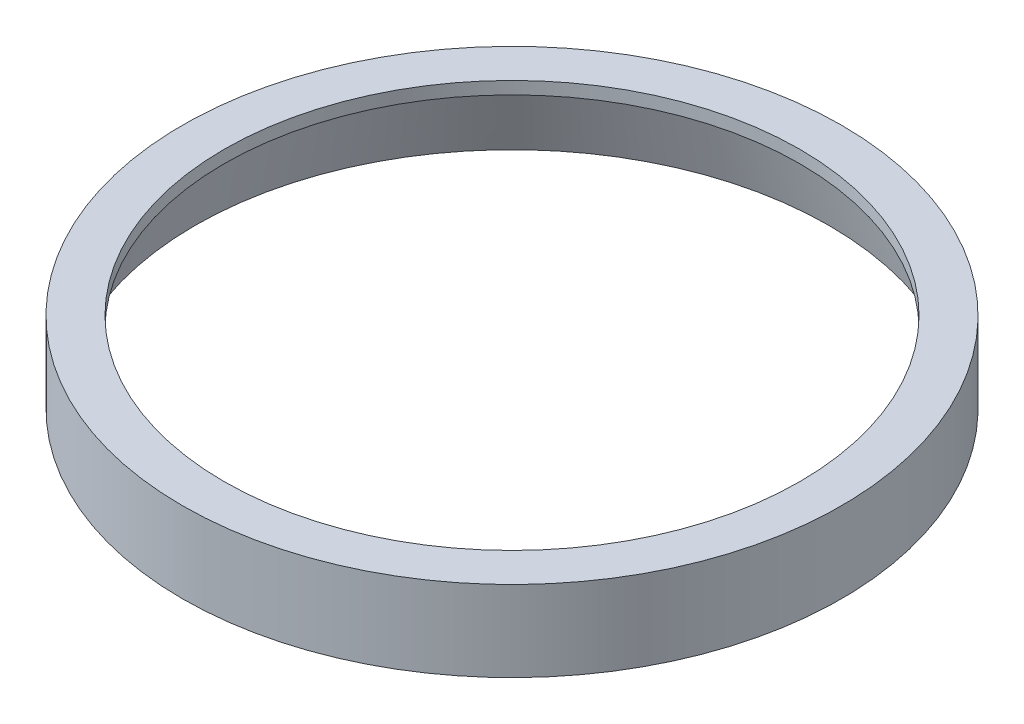
SolidWorks part; units mm, degrees
ref_plane "Front Plane" through (0, 0, 0) normal (0, 0, 1) x (1, 0, 0)
ref_plane "Top Plane" through (0, 0, 0) normal (0, 1, 0) x (1, 0, 0)
ref_plane "Right Plane" through (0, 0, 0) normal (1, 0, 0) x (0, 0, -1)
sketch "Sketch1" plane through (0, 0, 0) normal (0, 0, 1) x (1, 0, 0)
  line L0 (37.5, 0) -> (30.5, 0) construction
  line L1 (30.5, 0) -> (30.5, 1.45) construction
  line L2 (30.5, 1.45) -> (32.5, 1.45) construction
  line L3 (32.5, 1.45) -> (32.5, 8) construction
  line L4 (37.5, 0) -> (37.5, 2.2679) construction
  line L5 (37.5, 2.2679) -> (35.5, 9.7321) construction
  line L6 (34.5, 8) -> (32.5, 8) construction
  line L7 (34.5, 8) -> (35.5, 9.7321) construction
  line L8 (35.5, 9.7321) -> (35.5, 0) construction
  line L9 (34.5, 8) -> (34.5, 10) construction
  line L10 (32.5, 1.45) -> (32.5, 0) construction
  line L12 (0, 0) -> (0, 8.4748) construction
  line L13 (38, 2.3338) -> (35.9328, 10.0487)
  line L14 (34.5, 10) -> (34.5, 10.5) construction
  line L15 (38, 2.3338) -> (39.5, 2.3338)
  line L16 (39.5, 2.3338) -> (39.5, 12)
  line L17 (39.5, 12) -> (34.5, 12)
  line L18 (34.5, 12) -> (34.5, 10.5)
  line L19 (38, -0.5) -> (30, -0.5) construction
  line L20 (38, -0.5) -> (38, 2.3338) construction
  line L21 (30, -0.5) -> (30, 1.95) construction
  line L22 (30, 1.95) -> (32, 1.95) construction
  line L23 (32, 1.95) -> (32, 8) construction
  arc A0 (32.5, 8) -> (35.5, 9.7321) centre (34.5, 8) cw construction
  arc A1 (34.5, 10.5) -> (35.9328, 10.0487) centre (34.5, 8) cw
  arc A2 (32, 8) -> (35.9328, 10.0487) centre (34.5, 8) cw construction
  point P25 (0, 0)
revolve "Revolve1" add sketch "Sketch1" angle 360 about L12
equation "\"Lens_D1\"= 61mm'lens inner diameter"
equation "\"Slot_H\"= 1.45mm'height of connecting slot between lens and 3d printed parted"
equation "\"3D_H1\"= 10mm'height of 1st 3D printed piece"
equation "\"Slot_T\"= 2mm'thickness of connecting slot"
equation "\"3D_T1\"= 5mm'thickness of first 3D printed lense piece"
equation "\"F_T\"= 0.5mm'film thickness"
equation "\"3D_A1\"= 120deg'angle of contact for first 3d piece"
equation "\"3D_A2\"= 15deg'slope of side for first 3D printed piece"
equation "\"D1@Sketch1\"=\"Slot_T\""
equation "\"D2@Sketch1\"=\"Slot_H\""
equation "\"D4@Sketch1\"=\"3D_A1\""
equation "\"D5@Sketch1\"=\"3D_A2\""
equation "\"D6@Sketch1\"=\"3D_H1\""
equation "\"3D_R1\"= 2mm'top radius for 1st 3d printed piece"
equation "\"D8@Sketch1\"=\"3D_R1\""
equation "\"3D_T2\"= 1.5mm'thickness for 2nd 3D piece"
equation "\"D10@Sketch1\"=\"3D_T2\""
equation "\"D11@Sketch1\"=\"3D_T2\""
equation "\"D7@Sketch1\"=\"Lens_D1\"/2"
